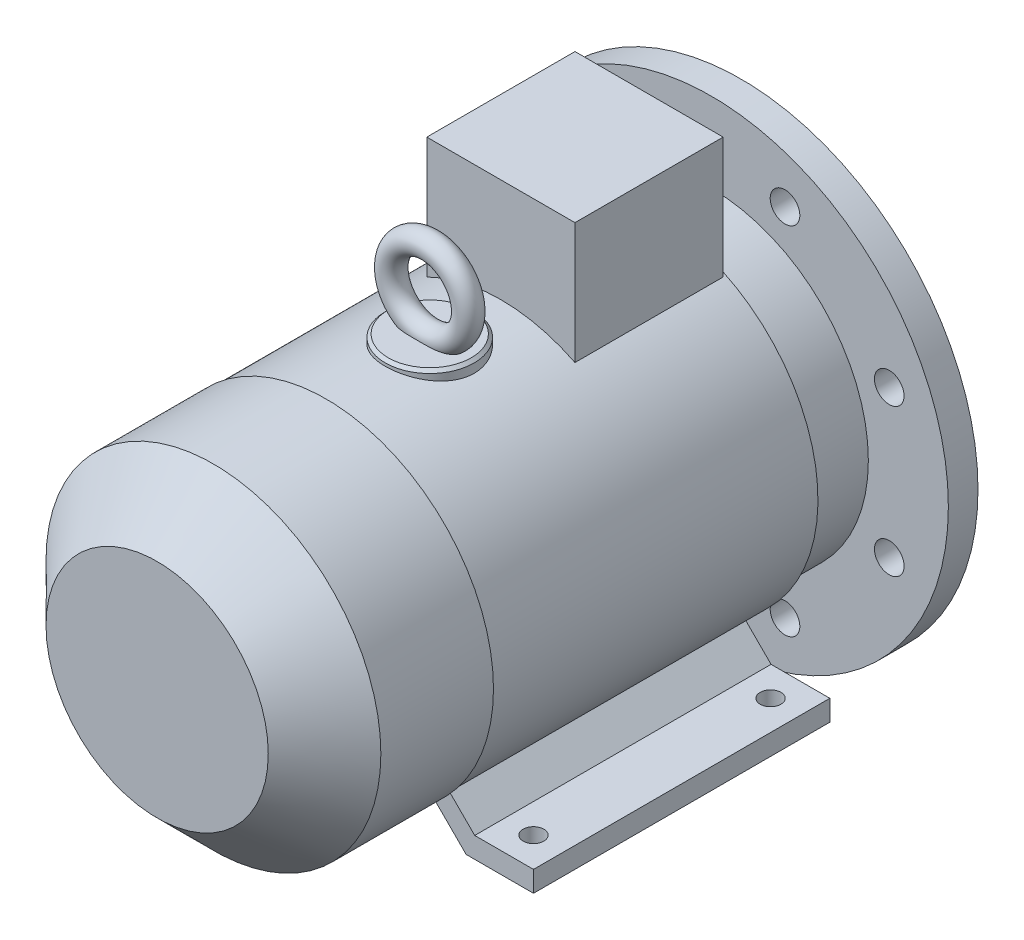
SolidWorks part; units mm, degrees
material "Ст.3 ГОСТ 380-88"
ref_plane "Спереди" through (0, 0, 0) normal (0, 0, 1) x (1, 0, 0)
ref_plane "Сверху" through (0, 0, 0) normal (0, 1, 0) x (1, 0, 0)
ref_plane "Справа" through (0, 0, 0) normal (1, 0, 0) x (0, 0, -1)
sketch "Эскиз1" plane through (0, 0, 0) normal (0, 0, 1) x (1, 0, 0)
  circle A0 centre (0, 0) radius 7
  dimension "D1" = 14
extrude "Вытянуть1" add sketch "Эскиз1" along normal blind 30
sketch "Эскиз2" plane through (0, 0, 0) normal (0, 0, -1) x (-1, 0, 0)
  line L0 (0, 0) -> (0, 8.0118) construction
  line L2 (-2.5, 9) -> (2.5, 9)
  line L3 (-2.5, 9) -> (-2.5, 4)
  line L4 (-2.5, 4) -> (2.5, 4)
  line L5 (2.5, 9) -> (2.5, 4)
  circle A8 centre (0, 0) radius 7 construction
  dimension "D1" = 5
  dimension "D2" = 5
  dimension "D3" = 16
extrude "Вытянуть2" add sketch "Эскиз2" against normal blind 20 and the other way blind 0.1
sketch "Эскиз3" plane through (0, 0, 30) normal (0, 0, 1) x (1, 0, 0)
  circle A0 centre (0, 0) radius 9
  dimension "D1" = 18
extrude "Вытянуть3" add sketch "Эскиз3" along normal blind 4
sketch "Эскиз4" plane through (0, 0, 30) normal (0, 0, -1) x (-1, 0, 0)
  circle A0 centre (0, 0) radius 80
  circle A1 centre (0, 0) radius 52
  dimension "D1" = 160
  dimension "D2" = 104
extrude "Вытянуть4" add sketch "Эскиз4" against normal blind 10
sketch "Эскиз5" plane through (0, 0, 34) normal (0, 0, 1) x (1, 0, 0)
  circle A0 centre (0, 0) radius 53
  dimension "D1" = 106
extrude "Вытянуть5" add sketch "Эскиз5" along normal blind 26
sketch "Эскиз7" plane through (0, 0, 34) normal (0, 0, -1) x (-1, 0, 0)
  circle A0 centre (0, 0) radius 55
  circle A1 centre (0, 0) radius 52
  dimension "D1" = 110
  dimension "D2" = 104
extrude "Вытянуть6" add sketch "Эскиз7" along normal blind 7.5
chamfer "Фаска1" distance 0.5 angle 45 2 edges at (-55, 0, 26.5) (0, -7, 0)
sketch "Эскиз8" plane through (0, 0, 30) normal (0, 0, -1) x (-1, 0, 0)
  line L0 (0, 0) -> (0, 92.1806) construction
  line L1 (0, 0) -> (-37.2596, 89.9525) construction
  circle A0 centre (-24.8744, 60.0522) radius 5
  circle A3 centre (24.8744, 60.0522) radius 5
  circle A4 centre (60.0522, 24.8744) radius 5
  circle A5 centre (60.0522, -24.8744) radius 5
  circle A6 centre (24.8744, -60.0522) radius 5
  circle A7 centre (-24.8744, -60.0522) radius 5
  circle A8 centre (-60.0522, -24.8744) radius 5
  circle A9 centre (-60.0522, 24.8744) radius 5
  dimension "D2" = 10
  dimension "D1" = 22.5
  dimension "D3" = 65
  dimension "D4" = 65
  dimension "D5" = 65
extrude "Вырез-Вытянуть1" cut sketch "Эскиз8" against normal through all
sketch "Эскиз10" plane through (0, 0, 60) normal (0, 0, 1) x (1, 0, 0)
  circle A0 centre (0, 0) radius 56
  dimension "D1" = 112
extrude "Вытянуть7" add sketch "Эскиз10" along normal blind 110
sketch "Эскиз11" plane through (0, 0, 170) normal (0, 0, 1) x (1, 0, 0)
  circle A0 centre (0, 0) radius 56.5
  dimension "D1" = 113
extrude "Вытянуть8" add sketch "Эскиз11" along normal blind 57
chamfer "Фаска2" distance 19 angle 45 1 edges at (56.5, 0, 227)
sketch "Эскиз12" plane through (0, 0, 60) normal (0, 0, -1) x (-1, 0, 0)
  line L0 (-60, -56) -> (-40.1691, -56)
  line L1 (-40.1691, -56) -> (-29.8002, -45.6311)
  line L2 (-60, -56) -> (-60, -63)
  line L3 (-60, -63) -> (-37.2696, -63)
  line L4 (-37.2696, -63) -> (-23.4613, -49.1916)
  line L5 (-23.4613, -49.1916) -> (-29.8002, -45.6311)
  line L6 (41.1159, -56) -> (60, -56)
  line L7 (60, -56) -> (60, -63)
  line L8 (60, -63) -> (38.2164, -63)
  line L9 (38.2164, -63) -> (24.4721, -49.2556)
  line L10 (24.4721, -49.2556) -> (30.3699, -45.254)
  line L11 (30.3699, -45.254) -> (41.1159, -56)
  line L12 (0, 0) -> (0, -81.8479) construction
  circle A0 centre (0, 0) radius 54.5 construction
  circle A2 centre (0, 0) radius 55 construction
  dimension "D1" = 120
  dimension "D2" = 63
  dimension "D3" = 7
  dimension "D4" = 7
  dimension "D5" = 7
  dimension "D6" = 45
  dimension "D7" = 45
extrude "Вытянуть9" add sketch "Эскиз12" against normal blind 100
sketch "Эскиз13" plane through (0, -63, 0) normal (0, -1, 0) x (1, 0, 0)
  line L0 (-79.1169, 70) -> (78.2403, 70) construction
  line L3 (-50, 70) -> (50, 70) construction
  line L4 (-50, 70) -> (-50, 150) construction
  circle A0 centre (-50, 70) radius 3.5
  circle A1 centre (50, 70) radius 3.5
  circle A2 centre (-50, 150) radius 3.5
  circle A3 centre (50, 150) radius 3.5
  dimension "D2" = 7
  dimension "D5" = 80
  dimension "D7" = 7
  dimension "D8" = 7
  dimension "D9" = 100
  dimension "D10" = 80
  dimension "D1" = 70
  dimension "D3" = 50
  dimension "D4" = 90
  dimension "D6" = 100
  dimension "D11" = 150
extrude "Вырез-Вытянуть2" cut sketch "Эскиз13" against normal up to next
sketch "Эскиз14" plane through (0, 0, 0) normal (0, 1, 0) x (1, 0, 0)
  line L0 (0, 0) -> (0, -245.6037) construction
  line L1 (-25, -61) -> (25, -61)
  line L2 (-25, -61) -> (-25, -111)
  line L3 (-25, -111) -> (25, -111)
  line L4 (25, -61) -> (25, -111)
  line L5 (0, 0) -> (0, -237.2756) construction
  line L6 (56, -60) -> (-56, -60) construction
  dimension "D1" = 50
  dimension "D2" = 50
  dimension "D3" = 1
extrude "Вытянуть10" add sketch "Эскиз14" along normal blind 91
sketch "Эскиз15" plane through (0, 0, 0) normal (0, 1, 0) x (1, 0, 0)
  line L0 (0, 0) -> (0, -234.2074) construction
  circle A0 centre (0, -135) radius 15
  dimension "D1" = 30
  dimension "D2" = 135
extrude "Вытянуть11" add sketch "Эскиз15" along normal blind 58
chamfer "Фаска3" distance 1 angle 45 1 edges at (0, 58, 150)
ref_plane "Плоскость1" through (0, 0, 135) normal (0, 0, 1) x (1, 0, 0)
sketch "Эскиз16" plane through (0, 0, 135) normal (0, 0, 1) x (1, 0, 0)
  line L0 (14, 58) -> (-14, 58) construction
  line L1 (0, 0) -> (0, 107.034) construction
  circle A0 centre (0, 71) radius 13
  dimension "D1" = 26
sketch "Эскиз17" plane through (0, 0, 0) normal (1, 0, 0) x (0, 0, -1)
  line L4 (-121, 58) -> (-149, 58) construction
  line L6 (-135, 0) -> (-135, 107.034) construction
  circle A0 centre (-135, 84) radius 4
  dimension "D1" = 8
  dimension "D2" = 26
sweep "По траектории1" add profiles "Эскиз17" path "Эскиз16"
sketch "Эскиз18" plane through (-25, 0, 0) normal (-1, 0, 0) x (0, 0, 1)
  line L0 (61, 91) -> (61, 50.1099) construction
  line L1 (61, 91) -> (111, 91) construction
  circle A0 centre (86, 69) radius 7
  dimension "D1" = 14
  dimension "D2" = 25
  dimension "D3" = 22
extrude "Вытянуть12" add sketch "Эскиз18" along normal blind 4
sketch "Эскиз19" plane through (-29, 0, 0) normal (-1, 0, 0) x (0, 0, 1)
  line L0 (86, 69) -> (86, 93.9665) construction
  line L1 (86, 78.815) -> (77.5, 73.9075)
  line L2 (77.5, 73.9075) -> (77.5, 64.0925)
  line L3 (77.5, 64.0925) -> (86, 59.185)
  line L4 (86, 59.185) -> (94.5, 64.0925)
  line L5 (94.5, 64.0925) -> (94.5, 73.9075)
  line L6 (94.5, 73.9075) -> (86, 78.815)
  circle A0 centre (86, 69) radius 8.5 construction
  circle A1 centre (86, 69) radius 7 construction
  dimension "D1" = 17
extrude "Вытянуть13" add sketch "Эскиз19" along normal blind 7
sketch "Эскиз20" plane through (-36, 0, 0) normal (-1, 0, 0) x (0, 0, 1)
  circle A0 centre (86, 69) radius 4
  circle A1 centre (86, 69) radius 7 construction
  dimension "D1" = 8
extrude "Вырез-Вытянуть3" cut sketch "Эскиз20" against normal blind 7
